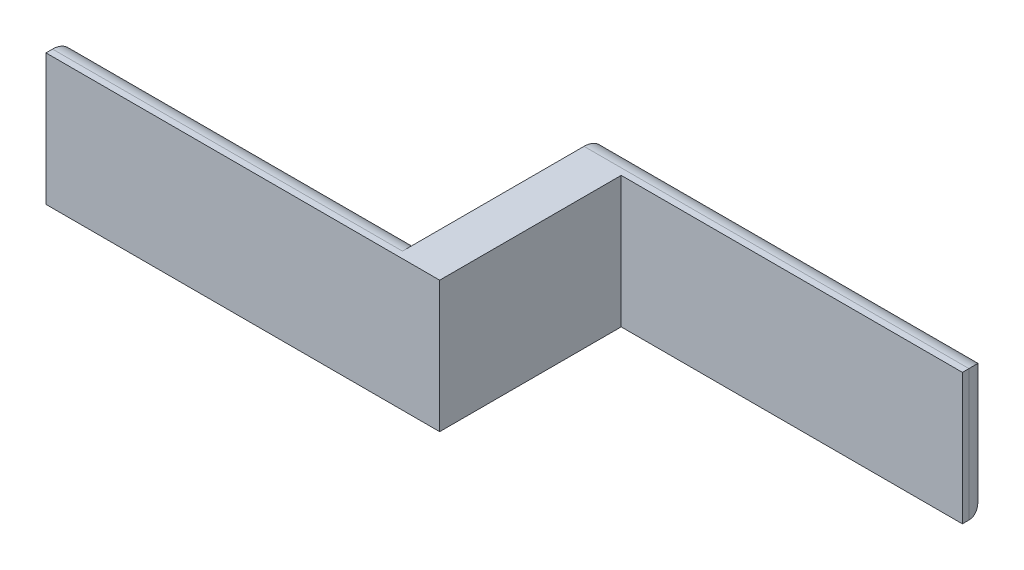
SolidWorks part; units mm, degrees
ref_plane "Front Plane" through (0, 0, 0) normal (0, 0, 1) x (1, 0, 0)
ref_plane "Top Plane" through (0, 0, 0) normal (0, 1, 0) x (1, 0, 0)
ref_plane "Right Plane" through (0, 0, 0) normal (1, 0, 0) x (0, 0, -1)
sketch "Sketch2" plane through (0, 0, 0) normal (0, 1, 0) x (1, 0, 0)
  line L1 (0, 0) -> (114.3, 0)
  line L2 (0, 0) -> (0, 8.255)
  line L3 (0, 8.255) -> (114.3, 8.255)
  line L4 (114.3, 0) -> (114.3, 8.255)
  line L5 (101.6, 52.705) -> (213.36, 52.705)
  line L6 (101.6, 52.705) -> (101.6, 60.96)
  line L7 (101.6, 60.96) -> (213.36, 60.96)
  line L8 (213.36, 52.705) -> (213.36, 60.96)
  line L9 (101.6, 52.705) -> (114.3, 52.705)
  line L10 (101.6, 52.705) -> (101.6, 8.255)
  line L11 (101.6, 8.255) -> (114.3, 8.255)
  line L12 (114.3, 52.705) -> (114.3, 8.255)
  dimension "D1" = 99.06
  dimension "D2" = 8.255
  dimension "D3" = 8.255
  dimension "D4" = 101.6
  dimension "D5" = 111.76
  dimension "D6" = 44.45
extrude "Boss-Extrude1" add sketch "Sketch2" along normal blind 38.1 contours L1 L4 L3 L2 | L5 L8 L7 L6 L3 | L12 L5 L10 L3
fillet "Fillet1" radius 6.35 5 edges at (50.8, 0, -8.255) (50.8, 38.1, -8.255) (213.36, 19.05, -60.96) (157.48, 0, -60.96) (157.48, 38.1, -60.96)
